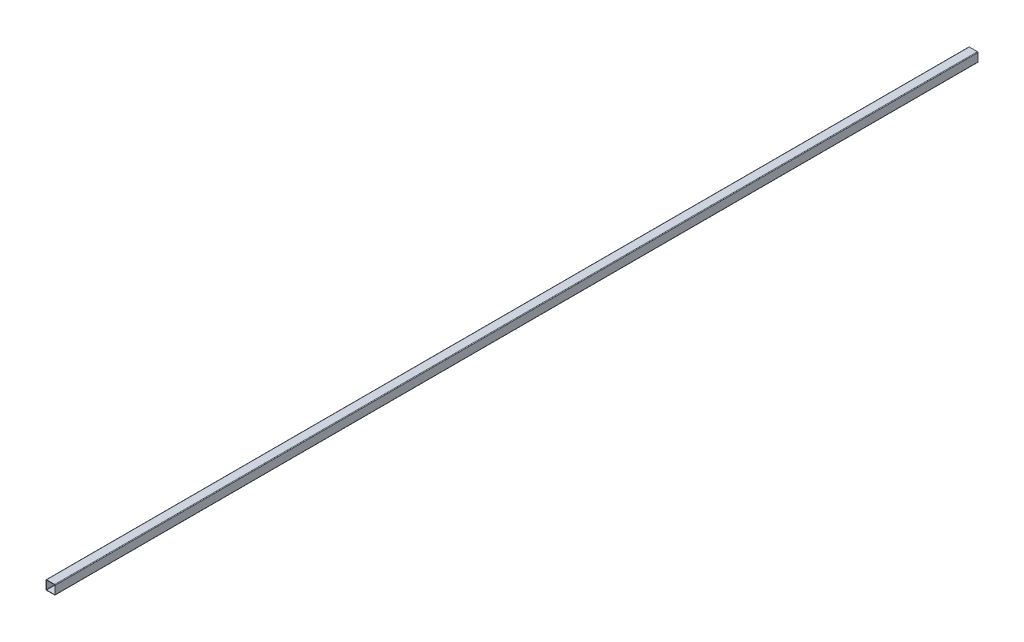
SolidWorks part; units mm, degrees
ref_plane "Спереди" through (0, 0, 0) normal (0, 0, 1) x (1, 0, 0)
ref_plane "Сверху" through (0, 0, 0) normal (0, 1, 0) x (1, 0, 0)
ref_plane "Справа" through (0, 0, 0) normal (1, 0, 0) x (0, 0, -1)
sketch "Эскиз1" plane through (0, 0, 0) normal (0, 0, 1) x (1, 0, 0)
  line L1 (-13, 14) -> (13, 14)
  line L2 (-14, 13) -> (-14, -13)
  line L3 (-13, -14) -> (13, -14)
  line L4 (14, 13) -> (14, -13)
  line L5 (-13, 15) -> (13, 15)
  line L6 (-15, 13) -> (-15, -13)
  line L7 (-13, -15) -> (13, -15)
  line L8 (15, 13) -> (15, -13)
  arc A0 (-14, -13) -> (-13, -14) centre (-13, -13) ccw
  arc A1 (13, -14) -> (14, -13) centre (13, -13) ccw
  arc A2 (13, 14) -> (14, 13) centre (13, 13) cw
  arc A3 (-13, 14) -> (-14, 13) centre (-13, 13) ccw
  arc A4 (-15, -13) -> (-13, -15) centre (-13, -13) ccw
  arc A5 (13, -15) -> (15, -13) centre (13, -13) ccw
  arc A6 (13, 15) -> (15, 13) centre (13, 13) cw
  arc A7 (-13, 15) -> (-15, 13) centre (-13, 13) ccw
  point P8 (-15, 0)
  point P9 (-14, 0)
  point P11 (0, 15)
  point P12 (0, 14)
  dimension "D1" = 1
  dimension "D2" = 2
  dimension "D3" = 30
  dimension "D4" = 1
extrude "Бобышка-Вытянуть1" add sketch "Эскиз1" along normal blind 3000
